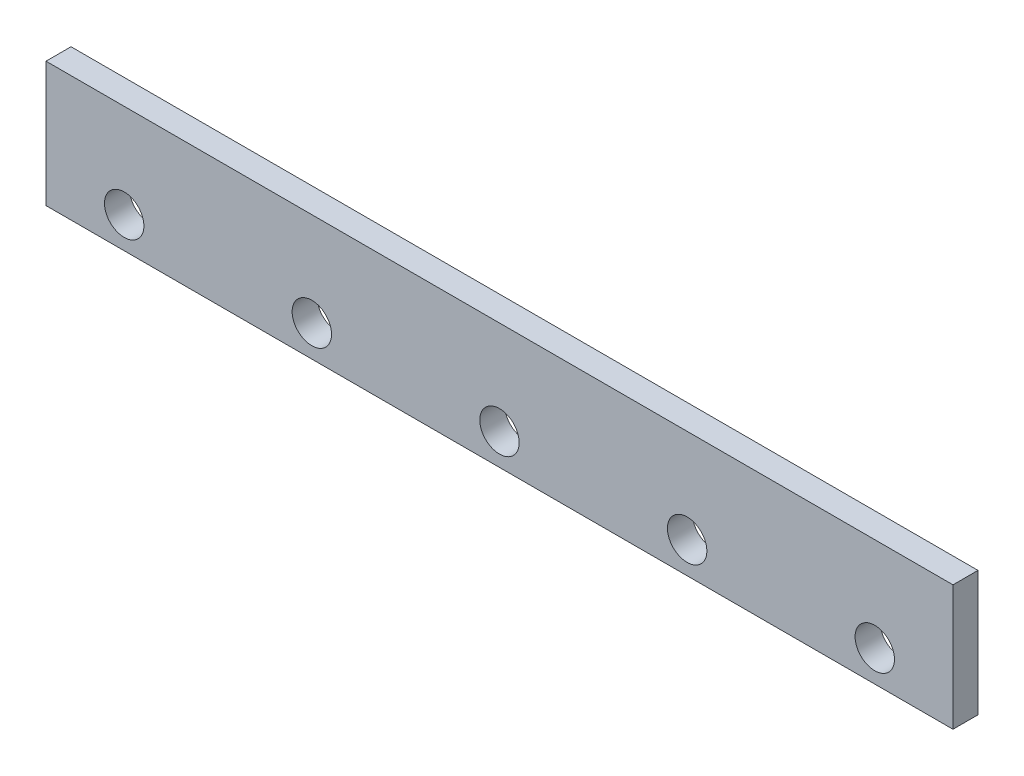
SolidWorks part; units mm, degrees
ref_plane "Front Plane" through (0, 0, 0) normal (0, 0, 1) x (1, 0, 0)
ref_plane "Top Plane" through (0, 0, 0) normal (0, 1, 0) x (1, 0, 0)
ref_plane "Right Plane" through (0, 0, 0) normal (1, 0, 0) x (0, 0, -1)
sketch "Sketch1" plane through (0, 0, 0) normal (0, 0, 1) x (1, 0, 0)
  line L1 (0, 0) -> (580, 0)
  line L2 (0, 0) -> (0, 80)
  line L3 (0, 80) -> (580, 80)
  line L4 (580, 0) -> (580, 80)
  circle A0 centre (50, 20) radius 12.6
  circle A1 centre (170, 20) radius 12.6
  circle A2 centre (410, 20) radius 12.6
  circle A3 centre (290, 20) radius 12.6
  circle A4 centre (530, 20) radius 12.6
  dimension "D4" = 20
  dimension "D5" = 25.2
  dimension "D11" = 25.2
  dimension "D12" = 25.2
  dimension "D13" = 25.2
  dimension "D14" = 25.2
  dimension "D1" = 580
  dimension "D2" = 80
  dimension "D3" = 50
  dimension "D6" = 120
  dimension "D7" = 120
  dimension "D8" = 120
  dimension "D9" = 120
  dimension "D10" = 50
  dimension "D15" = 20
extrude "Boss-Extrude1" add sketch "Sketch1" along normal blind 16
